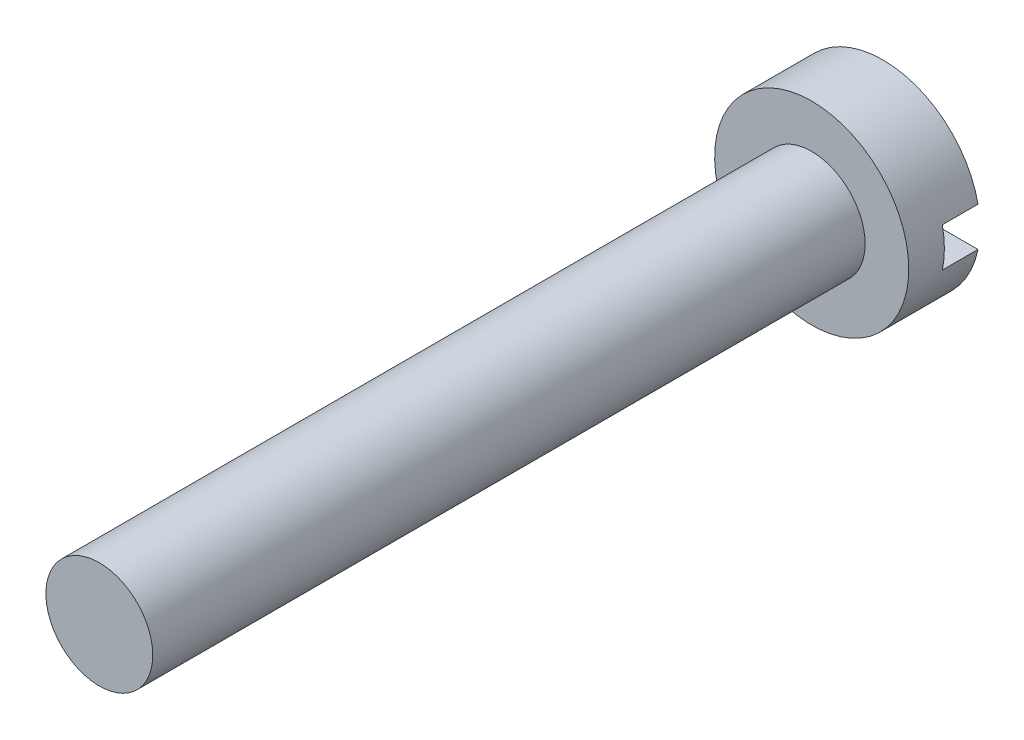
SolidWorks part; units mm, degrees
ref_plane "Front Plane" through (0, 0, 0) normal (0, 0, 1) x (1, 0, 0)
ref_plane "Top Plane" through (0, 0, 0) normal (0, 1, 0) x (1, 0, 0)
ref_plane "Right Plane" through (0, 0, 0) normal (1, 0, 0) x (0, 0, -1)
sketch "Sketch1" plane through (0, 0, 0) normal (0, 0, 1) x (1, 0, 0)
  circle A0 centre (0, 0) radius 2.725
extrude "Extrude1" add sketch "Sketch1" along normal blind 2
sketch "Sketch2" plane through (0, 0, 0) normal (0, 0, -1) x (-1, 0, 0)
  line L0 (-3.9013, 0) -> (3.4498, 0) construction
  line L1 (3.4498, 0) -> (3.4498, 0.55)
  line L2 (3.4498, 0.55) -> (-3.9013, 0.55)
  line L3 (-3.9013, 0.55) -> (-3.9013, -0.55)
  line L4 (-3.9013, -0.55) -> (3.4498, -0.55)
  line L5 (3.4498, -0.55) -> (3.4498, 0)
extrude "Cut-Extrude1" cut sketch "Sketch2" against normal blind 1
sketch "Sketch3" plane through (0, 0, 2) normal (0, 0, 1) x (1, 0, 0)
  circle A0 centre (0, 0) radius 1.5
extrude "Extrude2" add sketch "Sketch3" along normal blind 20
